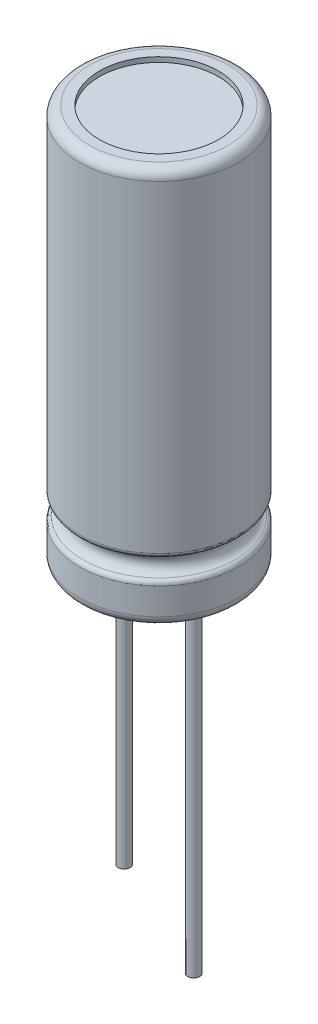
SolidWorks part; units mm, degrees
ref_plane "Front" through (0, 0, 0) normal (0, 0, 1) x (1, 0, 0)
ref_plane "Top" through (0, 0, 0) normal (0, 1, 0) x (1, 0, 0)
ref_plane "Right" through (0, 0, 0) normal (1, 0, 0) x (0, 0, -1)
sketch "Sketch1" plane through (0, 0, 0) normal (0, 1, 0) x (1, 0, 0)
  circle A0 centre (0, 0) radius 4
  dimension "D1" = 8
extrude "Base-Extrude" add sketch "Sketch1" along normal blind 20
sketch "Sketch2" plane through (0, 0, 0) normal (1, 0, 0) x (0, 0, -1)
  line L0 (-4, 20) -> (-4, 0) construction
  line L1 (-4, 3.0532) -> (-4, 2.0532)
  line L2 (0, 0) -> (0, 7.7627) construction
  line L3 (0, 20) -> (0, 0) construction
  arc A0 (-4, 2.0532) -> (-4, 3.0532) centre (-4, 2.5532) ccw
  dimension "D1" = 0.5
revolve "Cut-Revolve1" cut sketch "Sketch2" angle 360 about L2
fillet "Fillet1" radius 0.5 2 edges at (0, 0, 4) (0, 20, 4)
fillet "Fillet2" radius 0.25 2 edges at (0, 2.0532, -4) (0, 3.0532, -4)
sketch "Sketch4" plane through (0, 0, 0) normal (0, -1, 0) x (1, 0, 0)
  circle A0 centre (0, 0) radius 3
  dimension "D1" = 6
extrude "Cut-Extrude1" cut sketch "Sketch4" against normal blind 0.25
sketch "Sketch3" plane through (0, 0.25, 0) normal (0, -1, 0) x (1, 0, 0)
  circle A0 centre (-1.75, 0) radius 0.3
  circle A1 centre (1.75, 0) radius 0.3
  dimension "D1" = 0.6
  dimension "D2" = 1.75
  dimension "D3" = 3.5
extrude "Boss-Extrude1" add sketch "Sketch3" along normal blind 17.25
sketch "Sketch5" plane through (0, -17, 0) normal (0, -1, 0) x (1, 0, 0)
  circle A1 centre (-1.75, 0) radius 0.3
  circle A2 centre (-1.75, 0) radius 0.3
  dimension "D1" = 0
extrude "Cut-Extrude2" cut sketch "Sketch5" against normal blind 3
sketch "Sketch6" plane through (0, 20, 0) normal (0, 1, 0) x (-1, 0, 0)
  circle A0 centre (0, 0) radius 3
  dimension "D1" = 6
extrude "Cut-Extrude3" cut sketch "Sketch6" against normal blind 0.25
